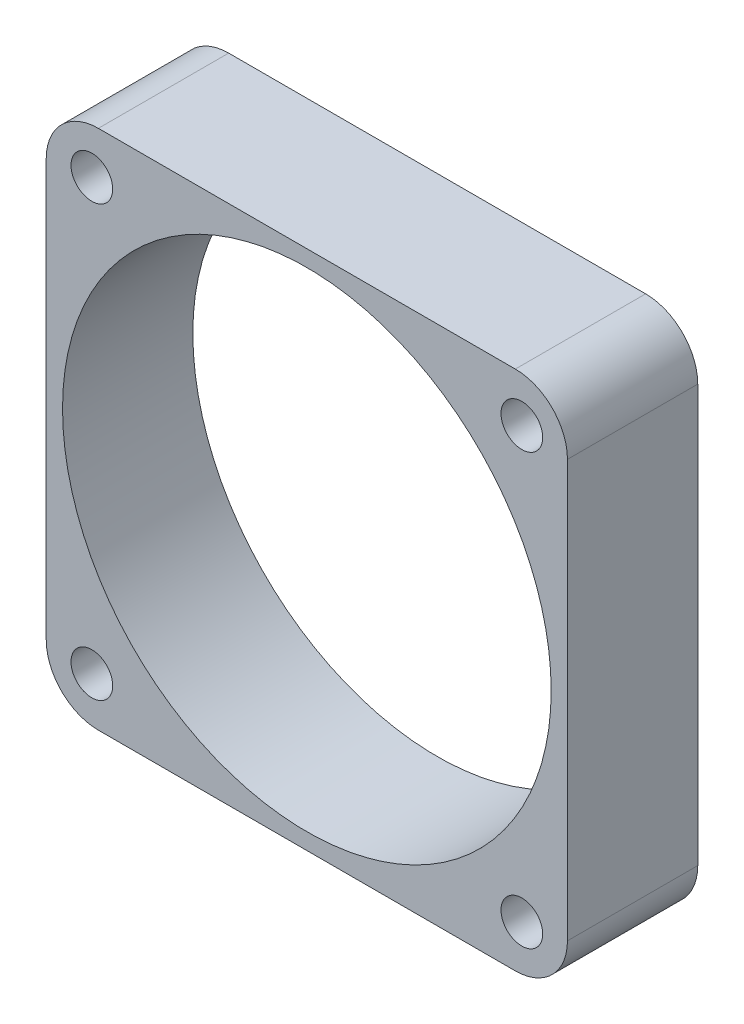
SolidWorks part; units mm, degrees
ref_plane "Спереди" through (0, 0, 0) normal (0, 0, 1) x (1, 0, 0)
ref_plane "Сверху" through (0, 0, 0) normal (0, 1, 0) x (1, 0, 0)
ref_plane "Справа" through (0, 0, 0) normal (1, 0, 0) x (0, 0, -1)
sketch "Эскиз1" plane through (0, 0, 0) normal (0, 0, 1) x (1, 0, 0)
  line L0 (4, 0) -> (36, 0)
  line L1 (0, 4) -> (0, 36)
  line L2 (40, 4) -> (40, 36)
  line L3 (4, 40) -> (36, 40)
  line L4 (3.5, 36.5) -> (36.5, 36.5) construction
  line L5 (3.5, 36.5) -> (3.5, 3.5) construction
  line L6 (36.5, 36.5) -> (36.5, 3.5) construction
  line L7 (3.5, 3.5) -> (36.5, 3.5) construction
  line L8 (20, 36.5) -> (20, 3.5) construction
  line L9 (36.5, 20) -> (3.5, 20) construction
  circle A0 centre (3.5, 36.5) radius 1.6
  circle A1 centre (36.5, 36.5) radius 1.6
  circle A2 centre (36.5, 3.5) radius 1.6
  circle A3 centre (3.5, 3.5) radius 1.6
  circle A4 centre (20, 20) radius 18.75
  arc A5 (0, 4) -> (4, 0) centre (4, 4) ccw
  arc A6 (36, 0) -> (40, 4) centre (36, 4) ccw
  arc A7 (40, 36) -> (36, 40) centre (36, 36) ccw
  arc A8 (4, 40) -> (0, 36) centre (4, 36) ccw
  point P21 (0, 0)
  point P24 (40, 0)
  point P29 (0, 40)
  dimension "D7" = 3.2
  dimension "D8" = 3.2
  dimension "D9" = 3.2
  dimension "D10" = 3.2
  dimension "D11" = 37.5
  dimension "D12" = 4
  dimension "D1" = 40
  dimension "D2" = 40
  dimension "D3" = 3.5
  dimension "D4" = 3.5
  dimension "D5" = 3.5
  dimension "D6" = 3.5
extrude "Бобышка-Вытянуть1" add sketch "Эскиз1" along normal blind 10
